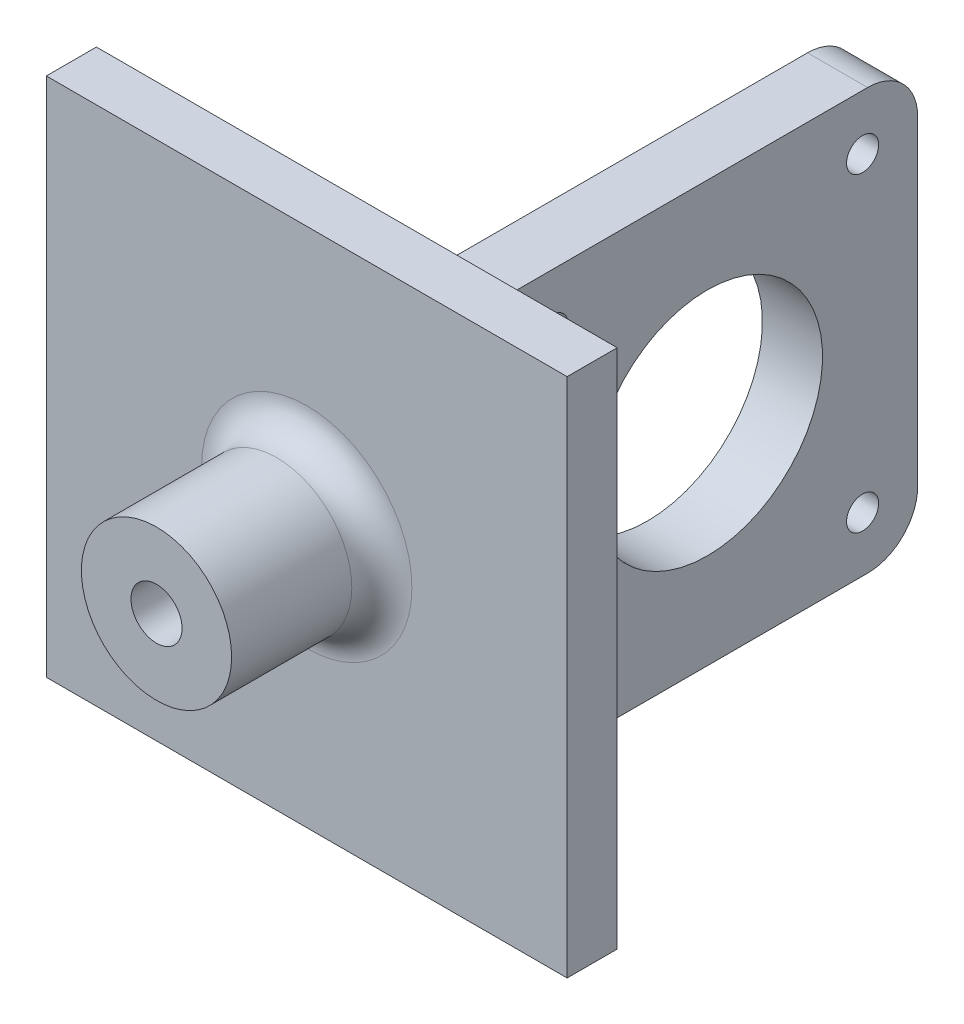
SolidWorks part; units mm, degrees
ref_plane "前视基准面" through (0, 0, 0) normal (0, 0, 1) x (1, 0, 0)
ref_plane "上视基准面" through (0, 0, 0) normal (0, 1, 0) x (1, 0, 0)
ref_plane "右视基准面" through (0, 0, 0) normal (1, 0, 0) x (0, 0, -1)
sketch "草图1" plane through (0, 0, 0) normal (0, 0, 1) x (1, 0, 0)
  circle A0 centre (-2.0389, 7.8849) radius 26
  dimension "D1" = 52
extrude "凸台-拉伸1" add sketch "草图1" along normal blind 5
sketch "草图2" plane through (0, 0, 5) normal (0, 0, 1) x (1, 0, 0)
  circle A0 centre (-2.0389, 7.8849) radius 7.5
  circle A1 centre (-2.0389, 7.8849) radius 2.55
  dimension "D1" = 5.1
  dimension "D2" = 15
extrude "凸台-拉伸2" add sketch "草图2" along normal blind 15 contours A0 | A1
sketch "草图3" plane through (0, 0, 0) normal (0, 0, -1) x (-1, 0, 0)
  line L0 (-23.9611, 7.8849) -> (28.0389, 7.8849)
  circle A0 centre (2.0389, 7.8849) radius 26 construction
ref_plane "基准面1" through (-28.0389, 0, 0) normal (-1, 0, 0) x (0, 0, 1)
sketch "草图4" plane through (-28.0389, 0, 0) normal (-1, 0, 0) x (0, 0, 1)
  line L0 (5, 7.8849) -> (20, 7.8849) construction
  line L1 (20, 15.3849) -> (5, 15.3849) construction
  line L2 (20, 15.3849) -> (20, 0.3849) construction
  line L3 (20, 0.3849) -> (5, 0.3849) construction
  line L4 (5, 15.3849) -> (5, 0.3849) construction
  circle A0 centre (12.5, 7.8849) radius 1.6
  dimension "D1" = 3.2
extrude "切除-拉伸1" cut sketch "草图4" against normal blind 20
sketch "草图6" plane through (0, 0, 0) normal (0, 0, -1) x (-1, 0, 0)
  line L0 (-23.9611, 7.8849) -> (28.0389, 7.8849) construction
  circle A0 centre (2.0389, 7.8849) radius 40.1586
  circle A1 centre (2.0389, 7.8849) radius 26
extrude "凸台-拉伸4" add sketch "草图6" against normal blind 5 contours A0
sketch "草图7" plane through (0, 0, 0) normal (0, 0, -1) x (-1, 0, 0)
  line L1 (-23.9611, 33.8849) -> (28.0389, 33.8849)
  line L2 (-23.9611, 33.8849) -> (-23.9611, -18.1151)
  line L3 (-23.9611, -18.1151) -> (28.0389, -18.1151)
  line L4 (28.0389, 33.8849) -> (28.0389, -18.1151)
  circle A0 centre (2.0389, 7.8849) radius 40.1586
  circle A1 centre (2.0389, 7.8849) radius 26 construction
  circle A2 centre (2.0389, 7.8849) radius 40.1586 construction
extrude "切除-拉伸2" cut sketch "草图7" against normal blind 5 contours A0 | L2 L1 L4 L3
sketch "草图8" plane through (0, 0, 0) normal (0, 0, -1) x (-1, 0, 0)
  line L1 (-8.9611, 28.8849) -> (-2.9611, 28.8849)
  line L2 (-8.9611, 28.8849) -> (-8.9611, -13.1151)
  line L3 (-8.9611, -13.1151) -> (-2.9611, -13.1151)
  line L4 (-2.9611, 28.8849) -> (-2.9611, -13.1151)
  line L6 (-23.9611, 33.8849) -> (-23.9611, -18.1151) construction
  line L7 (-23.9611, 33.8849) -> (28.0389, 33.8849) construction
  dimension "D1" = 6
  dimension "D2" = 15
  dimension "D3" = 42
  dimension "D4" = 5
extrude "凸台-拉伸5" add sketch "草图8" along normal blind 45
sketch "草图9" plane through (8.9611, 0, 0) normal (1, 0, 0) x (0, 0, -1)
  line L0 (3, 28.8849) -> (3, -13.1151) construction
  line L1 (45, 28.8849) -> (0, 28.8849) construction
  line L2 (45, -13.1151) -> (0, -13.1151) construction
  line L3 (0, 28.8849) -> (0, -13.1151) construction
  line L4 (45, 28.8849) -> (45, -13.1151) construction
  line L5 (3, 28.8849) -> (45, -13.1151) construction
  line L6 (24, 7.8849) -> (24, 28.8849) construction
  line L9 (8.5, 23.3849) -> (39.5, 23.3849) construction
  line L10 (8.5, 23.3849) -> (8.5, -7.6151) construction
  line L11 (8.5, -7.6151) -> (39.5, -7.6151) construction
  line L12 (39.5, 23.3849) -> (39.5, -7.6151) construction
  line L13 (24, 7.8849) -> (45, 7.8849) construction
  circle A0 centre (24, 7.8849) radius 11.5
  circle A1 centre (39.5, 23.3849) radius 1.6
  circle A2 centre (8.5, -7.6151) radius 1.6
  circle A3 centre (39.5, -7.6151) radius 1.6
  circle A4 centre (8.5, 23.3849) radius 1.6
  point P19 (24, 23.3849)
  point P20 (39.5, 7.8849)
  dimension "D3" = 23
  dimension "D6" = 3.2
  dimension "D1" = 3
  dimension "D2" = 42
  dimension "D4" = 31
  dimension "D5" = 31
extrude "切除-拉伸3" cut sketch "草图9" against normal blind 10
fillet "圆角1" radius 5 2 edges at (5.9611, -13.1151, -45) (5.9611, 28.8849, -45)
fillet "圆角2" radius 3 5 edges at (8.9611, 7.8849, 0) (5.9611, 28.8849, 0) (5.9611, -13.1151, 0) (5.4611, 7.8849, 5) (2.9611, 7.8849, 0)
